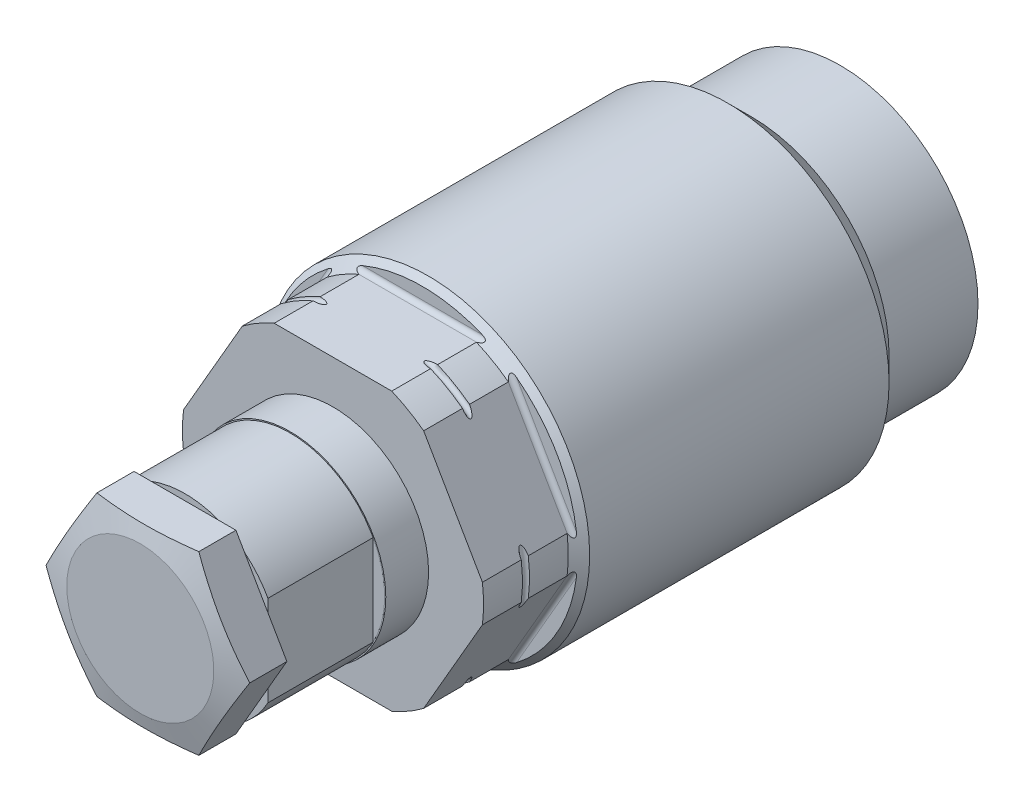
SolidWorks part; units mm, degrees
material "Alloy Steel"
ref_plane "Front Plane" through (0, 0, 0) normal (0, 0, 1) x (1, 0, 0)
ref_plane "Top Plane" through (0, 0, 0) normal (0, 1, 0) x (1, 0, 0)
ref_plane "Right Plane" through (0, 0, 0) normal (1, 0, 0) x (0, 0, -1)
sketch "Sketch1" plane through (0, 0, 0) normal (1, 0, 0) x (0, 0, -1)
  line L0 (0, 0) -> (122.3375, 0) construction
  line L1 (0, 0) -> (0, 14.8717)
  line L6 (0, 14.8717) -> (-9.6012, 14.8717)
  line L7 (-9.6012, 14.8717) -> (-12.1412, 17.4117)
  line L8 (-12.1412, 17.4117) -> (-44.4627, 17.4117)
  line L9 (-44.4627, 17.4117) -> (-45.6184, 16.256)
  line L10 (-45.6184, 16.256) -> (-54.7624, 16.256)
  line L11 (-54.7624, 16.256) -> (-54.7624, 0)
  line L12 (0, 0) -> (-54.7624, 0)
  dimension "D5" = 29.7434
  dimension "D6" = 9.6012
  dimension "D7" = 34.8234
  dimension "D8" = 45
  dimension "D9" = 54.7624
  dimension "D10" = 32.512
  dimension "D11" = 45
  dimension "D12" = 9.144
revolve "Revolve1" add sketch "Sketch1" angle 360 about L0
sketch "Sketch2" plane through (0, 0, 0) normal (1, 0, 0) x (0, 0, -1)
  line L0 (0, 0) -> (-47.105, 0) construction
  line L1 (-54.7624, 14.9669) -> (-45.6184, 14.9669)
  line L2 (-54.7624, 16.256) -> (-54.7624, -16.256) construction
  line L3 (-45.1104, 15.4749) -> (-45.1104, 18.1419)
  line L4 (-45.1104, 18.1419) -> (-54.7624, 18.1419)
  line L5 (-54.7624, 18.1419) -> (-54.7624, 14.9669)
  arc A0 (-45.1104, 15.4749) -> (-45.6184, 14.9669) centre (-45.6184, 15.4749) cw
  dimension "D4" = 0.508
  dimension "D1" = 29.9339
  dimension "D2" = 9.652
  dimension "D3" = 3.175
extrude "Cut-Extrude1" cut sketch "Sketch2" against normal through all and the other way through all
pattern_circular "CirPattern1" count 6 over 360 about axis through (0, 0, 0) along (0, 0, 1) of "Cut-Extrude1"
sketch "Sketch3" plane through (0, 0, 0) normal (1, 0, 0) x (0, 0, -1)
  line L0 (0, 0) -> (-60.8041, 0) construction
  line L1 (-75.565, 0) -> (-75.565, 7.9375) construction
  line L2 (-70.739, 10.3251) -> (-54.7624, 10.3251)
  line L3 (-54.7624, 1.9893) -> (-54.7624, 12.9776) construction
  line L4 (-54.7624, 10.3251) -> (-54.7624, 0)
  line L5 (-54.7624, 1.9893) -> (-54.7624, -1.9893) construction
  line L6 (-54.7624, 0) -> (-70.739, 0)
  line L7 (-70.739, 10.3251) -> (-70.739, 0)
  line L8 (0, -14.8717) -> (0, 14.8717) construction
  dimension "D1" = 4.826
  dimension "D2" = 20.6502
  dimension "D3" = 75.565
revolve "Revolve2" add sketch "Sketch3" angle 360 about L0
sketch "Sketch4" plane through (0, 0, 70.739) normal (0, 0, 1) x (1, 0, 0)
  circle A0 centre (0, 0) radius 5.9944
  circle A1 centre (0, 0) radius 10.3251 construction
  dimension "D1" = 11.9888
extrude "Cut-Extrude2" cut sketch "Sketch4" against normal blind 7.874
sketch "Sketch5" plane through (0, 0, 0) normal (1, 0, 0) x (0, 0, -1)
  line L0 (-54.7624, 14.9669) -> (-54.7624, 12.9776) construction
  line L1 (0, 0) -> (-52.6213, 0) construction
  line L2 (-50.5714, 19.431) -> (-50.5714, 16.256)
  line L3 (-49.8094, 19.431) -> (-49.8094, 16.256)
  line L4 (-50.5714, 19.431) -> (-49.8094, 19.431)
  arc A0 (-50.5714, 16.256) -> (-49.8094, 16.256) centre (-50.1904, 16.256) ccw
  dimension "D3" = 0.762
  dimension "D1" = 4.572
  dimension "D2" = 16.256
  dimension "D4" = 3.175
revolve "Cut-Revolve1" cut sketch "Sketch5" angle 360 about L1
sketch "Sketch10" plane through (0, 0, 0) normal (0, 1, 0) x (1, 0, 0)
  line L0 (0, 0) -> (0, -56.3853) construction
  line L1 (10.3251, -70.739) -> (10.3251, -54.7624) construction
  line L2 (8.9535, -70.739) -> (10.3251, -70.739)
  line L3 (8.9535, -70.739) -> (8.9535, -59.3852)
  line L4 (8.9535, -59.3852) -> (10.3251, -59.3852)
  line L5 (10.3251, -70.739) -> (10.3251, -59.3852)
  line L6 (-10.3251, -70.739) -> (10.3251, -70.739) construction
  line L7 (-10.3251, -70.739) -> (-10.3251, -59.3852)
  line L8 (-8.9535, -59.3852) -> (-10.3251, -59.3852)
  line L9 (-8.9535, -70.739) -> (-8.9535, -59.3852)
  line L10 (-8.9535, -70.739) -> (-10.3251, -70.739)
  dimension "D1" = 17.907
  dimension "D2" = 11.3538
extrude "Cut-Extrude3" cut sketch "Sketch10" against normal through all and the other way through all
sketch "Sketch11" plane through (0, 0, 70.739) normal (0, 0, 1) x (1, 0, 0)
  line L1 (5.4993, 9.525) -> (-5.4993, 9.525)
  line L2 (-5.4993, 9.525) -> (-10.9985, 0)
  line L3 (-10.9985, 0) -> (-5.4993, -9.525)
  line L4 (-5.4993, -9.525) -> (5.4993, -9.525)
  line L5 (5.4993, -9.525) -> (10.9985, 0)
  line L6 (10.9985, 0) -> (5.4993, 9.525)
  circle A0 centre (0, 0) radius 9.525 construction
  dimension "D1" = 19.05
extrude "Extrude2" add sketch "Sketch11" along normal blind 4.826
sketch "Sketch12" plane through (0, 0, 0) normal (0, 1, 0) x (1, 0, 0)
  line L0 (-10.9985, -74.7448) -> (-10.9985, -75.565)
  line L1 (-10.9985, -75.565) -> (-10.9985, -70.739) construction
  line L2 (-10.9985, -75.565) -> (-7.9375, -75.565)
  line L3 (-5.4993, -75.565) -> (-10.9985, -75.565) construction
  line L4 (-7.9375, -75.565) -> (-10.9985, -74.7448)
  line L5 (0, 0) -> (0, -66.9815) construction
  dimension "D1" = 15
  dimension "D2" = 15.875
revolve "Cut-Revolve3" cut sketch "Sketch12" angle 360 about L5
sketch "Sketch13" plane through (0, 0, 0) normal (1, 0, 0) x (0, 0, -1)
  line L0 (0, 0) -> (-75.565, 0) construction
  line L1 (-75.565, 7.9375) -> (-75.565, -7.9375) construction
  line L2 (-59.385, 10.3251) -> (-59.385, 10.2)
  line L4 (-54.7624, 10.3251) -> (-70.739, 10.3251) construction
  line L5 (-59.385, 10.2) -> (-70.739, 10.2)
  line L7 (-70.739, 10.3251) -> (-59.385, 10.3251)
  line L8 (-70.739, 10.2) -> (-70.739, 10.3251)
  dimension "D1" = 11.354
  dimension "D2" = 20.4
revolve "Cut-Revolve4" cut sketch "Sketch13" angle 360 about L0
